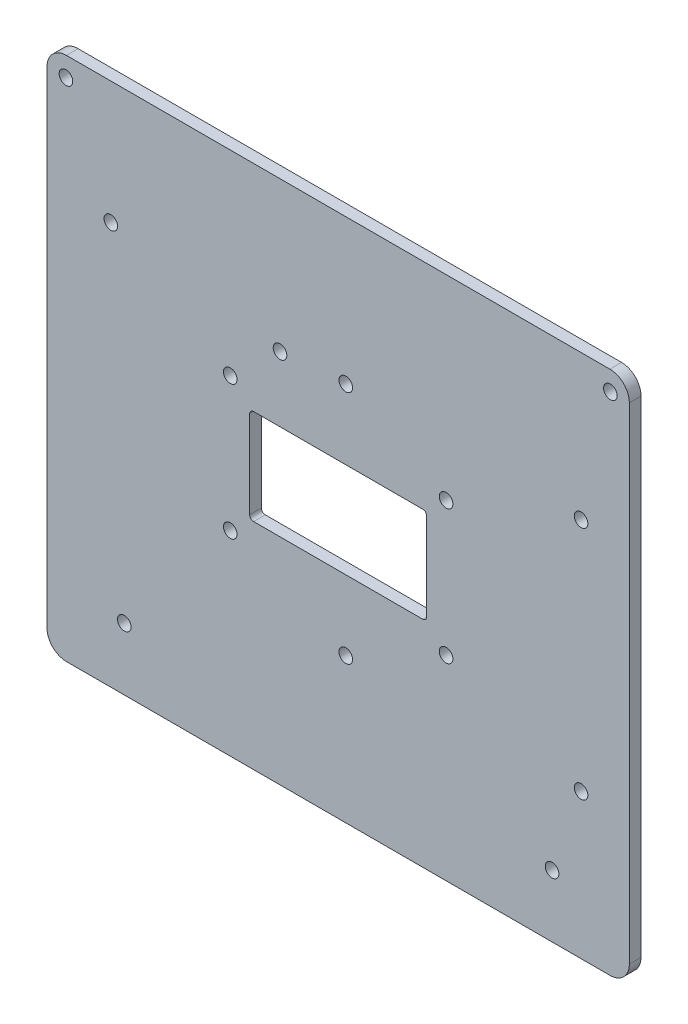
SolidWorks part; units mm, degrees
ref_plane "Plan de face" through (0, 0, 0) normal (0, 0, 1) x (1, 0, 0)
ref_plane "Plan de dessus" through (0, 0, 0) normal (0, 1, 0) x (1, 0, 0)
ref_plane "Plan de droite" through (0, 0, 0) normal (1, 0, 0) x (0, 0, -1)
sketch "Esquisse1" plane through (0, 0, 0) normal (0, 0, 1) x (1, 0, 0)
  line L0 (55, -67.5) -> (55, -51.5) construction
  line L1 (-74.875, 67.5) -> (74.875, 67.5)
  line L2 (-74.875, 67.5) -> (-74.875, -67.5)
  line L3 (-74.875, -67.5) -> (74.875, -67.5)
  line L4 (74.875, 67.5) -> (74.875, -67.5)
  line L5 (55, -51.5) -> (74.875, -51.5) construction
  line L6 (0, 0) -> (0, -67.5) construction
  line L7 (70, 62.5) -> (-70, 62.5) construction
  line L8 (-55, -40) -> (-62.4583, -40) construction
  line L9 (-62.4583, 40) -> (-10.4583, 40) construction
  line L10 (-62.4583, 40) -> (-62.4583, -40) construction
  line L11 (-62.4583, -40) -> (-10.4583, -40) construction
  line L12 (-10.4583, 40) -> (-10.4583, -40) construction
  line L13 (-62.4583, 36) -> (-58.4583, 36) construction
  line L14 (-58.4583, 36) -> (-58.4583, 40) construction
  line L15 (-10.4583, 0) -> (1.9583, 0) construction
  line L16 (-62.4583, 0) -> (-74.875, 0) construction
  line L17 (-58.4583, 36) -> (-58.4583, 29) construction
  line L18 (1.9583, 30.25) -> (62.4583, 30.25) construction
  line L19 (1.9583, 30.25) -> (1.9583, -30.25) construction
  line L20 (1.9583, -30.25) -> (62.4583, -30.25) construction
  line L21 (62.4583, 30.25) -> (62.4583, -30.25) construction
  line L22 (-58.4583, 29) -> (-14.9583, 29) construction
  line L23 (62.4583, 0) -> (74.875, 0) construction
  line L24 (-27.75, 17.25) -> (-27.75, -17.25) construction
  line L25 (-22.75, 12.25) -> (22.75, 12.25)
  line L26 (-22.75, 12.25) -> (-22.75, -12.25)
  line L27 (-22.75, -12.25) -> (22.75, -12.25)
  line L28 (22.75, 12.25) -> (22.75, -12.25)
  line L29 (-27.75, -17.25) -> (27.75, -17.25) construction
  line L30 (27.75, 17.25) -> (27.75, -17.25) construction
  line L31 (-27.75, 17.25) -> (27.75, 17.25) construction
  circle A6 centre (-70, 62.5) radius 1.75
  circle A7 centre (70, 62.5) radius 1.75
  circle A8 centre (55, -51.5) radius 1.75
  circle A9 centre (-55, -51.5) radius 1.75
  circle A10 centre (-58.4583, 36) radius 1.75
  circle A11 centre (-14.9583, 29) radius 1.75
  circle A12 centre (1.9583, 30.25) radius 1.75
  circle A13 centre (62.4583, 30.25) radius 1.75
  circle A14 centre (62.4583, -30.25) radius 1.75
  circle A15 centre (1.9583, -30.25) radius 1.75
  circle A16 centre (-27.75, 17.25) radius 1.75
  circle A17 centre (27.75, 17.25) radius 1.75
  circle A18 centre (27.75, -17.25) radius 1.75
  circle A19 centre (-27.75, -17.25) radius 1.75
  point P4 (0, 67.5)
  point P5 (-74.875, 0)
  point P26 (0, 62.5)
  point P32 (1.9583, 0)
  point P41 (-10.4583, 0)
  point P52 (0, 12.25)
  point P53 (-22.75, 0)
  dimension "D5" = 16
  dimension "D9" = 5
  dimension "D3" = 3.5
  dimension "D1" = 135
  dimension "D2" = 149.75
  dimension "D4" = 19.875
  dimension "D7" = 52
  dimension "D8" = 140
  dimension "D10" = 4
  dimension "D11" = 43.5
  dimension "D6" = 80
  dimension "D12" = 7
  dimension "D13" = 60.5
  dimension "D14" = 24.5
  dimension "D15" = 45.5
  dimension "D17" = 60.5
  dimension "D16" = 5
extrude "Boss.-Extru.1" add sketch "Esquisse1" along normal blind 3
fillet "Congé1" radius 5 4 edges at (74.875, -67.5, 1.5) (-74.875, -67.5, 1.5) (-74.875, 67.5, 1.5) (74.875, 67.5, 1.5)
fillet "Congé2" radius 1 4 edges at (22.75, 12.25, 1.5) (22.75, -12.25, 1.5) (-22.75, 12.25, 1.5) (-22.75, -12.25, 1.5)
